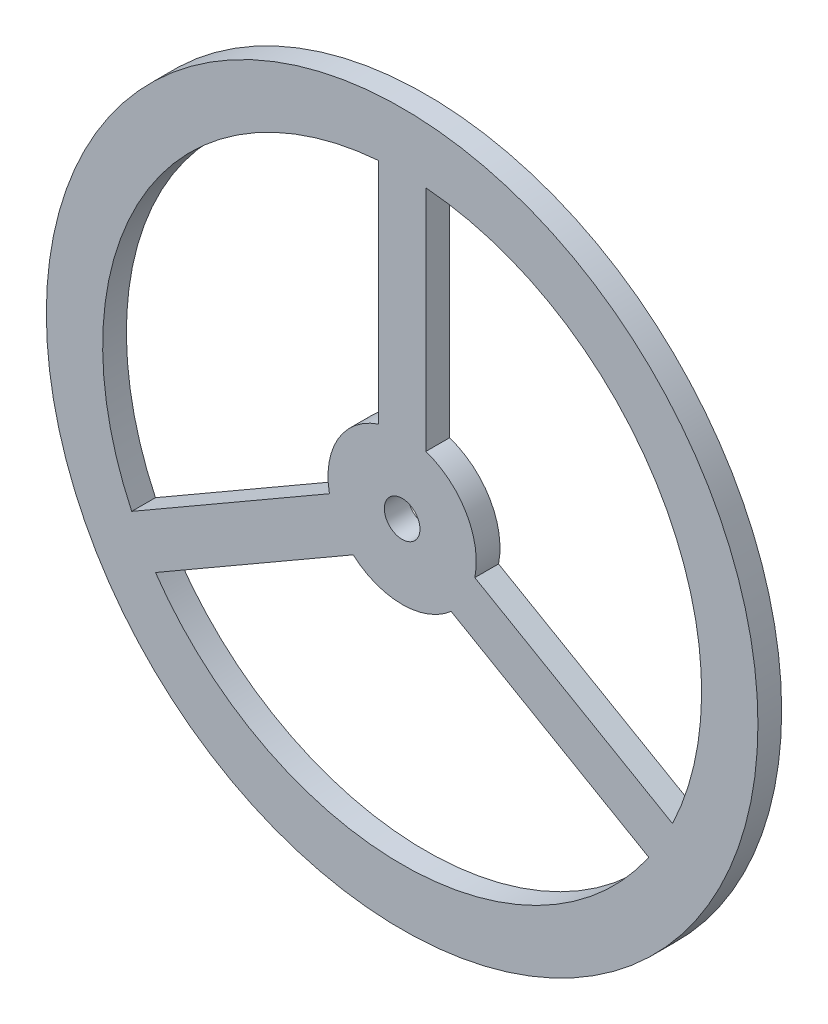
SolidWorks part; units mm, degrees
material "3003 合金"
ref_plane "前视基准面" through (0, 0, 0) normal (0, 0, 1) x (1, 0, 0)
ref_plane "上视基准面" through (0, 0, 0) normal (0, 1, 0) x (1, 0, 0)
ref_plane "右视基准面" through (0, 0, 0) normal (1, 0, 0) x (0, 0, -1)
sketch "草图1" plane through (0, 0, 0) normal (0, 0, 1) x (1, 0, 0)
  line L0 (-4, 11.8427) -> (-4, 50.3413)
  line L1 (0, 0) -> (0, 49.7006) construction
  line L2 (4, 11.8427) -> (4, 50.3413)
  line L3 (12.2561, -2.4573) -> (45.5969, -21.7066)
  line L4 (8.2561, -9.3855) -> (41.5969, -28.6348)
  line L5 (-8.2561, -9.3855) -> (-41.5969, -28.6348)
  line L6 (-12.2561, -2.4573) -> (-45.5969, -21.7066)
  circle A0 centre (0, 0) radius 60
  circle A1 centre (0, 0) radius 3
  arc A2 (-4, 50.3413) -> (-45.5969, -21.7066) centre (0, 0) ccw
  arc A3 (-4, 11.8427) -> (-12.2561, -2.4573) centre (0, 0) ccw
  arc A4 (-41.5969, -28.6348) -> (41.5969, -28.6348) centre (0, 0) ccw
  arc A5 (45.5969, -21.7066) -> (4, 50.3413) centre (0, 0) ccw
  arc A6 (12.2561, -2.4573) -> (4, 11.8427) centre (0, 0) ccw
  arc A7 (-8.2561, -9.3855) -> (8.2561, -9.3855) centre (0, 0) ccw
  dimension "D1" = 120
  dimension "D2" = 25
  dimension "D3" = 101
  dimension "D7" = 6
  dimension "D4" = 4
  dimension "D5" = 4
  dimension "D6" = 3
extrude "凸台-拉伸1" add sketch "草图1" along normal blind 4
